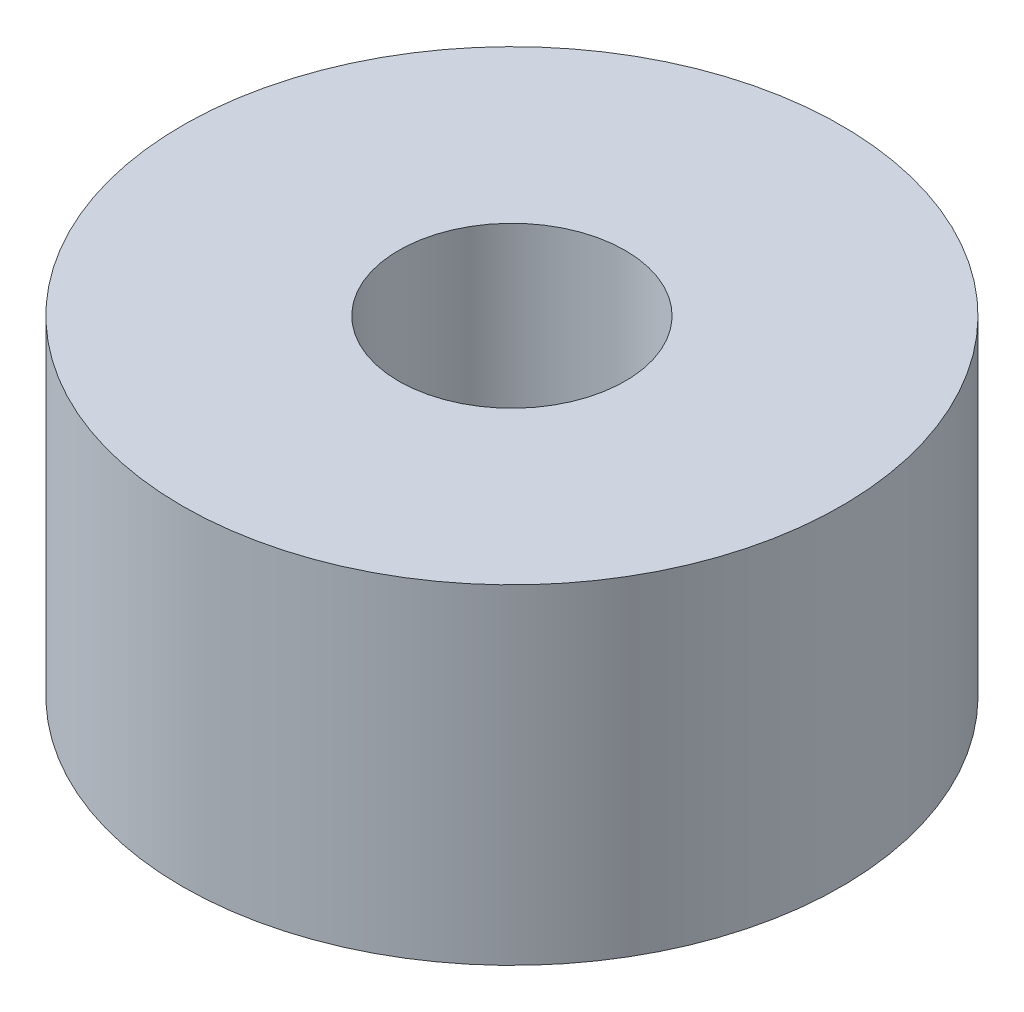
SolidWorks part; units mm, degrees
ref_plane "Front Plane" through (0, 0, 0) normal (0, 0, 1) x (1, 0, 0)
ref_plane "Top Plane" through (0, 0, 0) normal (0, 1, 0) x (1, 0, 0)
ref_plane "Right Plane" through (0, 0, 0) normal (1, 0, 0) x (0, 0, -1)
sketch "Sketch1" plane through (0, 0, 0) normal (0, 1, 0) x (1, 0, 0)
  circle A0 centre (0, 0) radius 2.1828
  circle A1 centre (0, 0) radius 6.35
  dimension "D1" = 4.3656
  dimension "D2" = 12.7
extrude "Boss-Extrude1" add sketch "Sketch1" along normal blind 6.35
